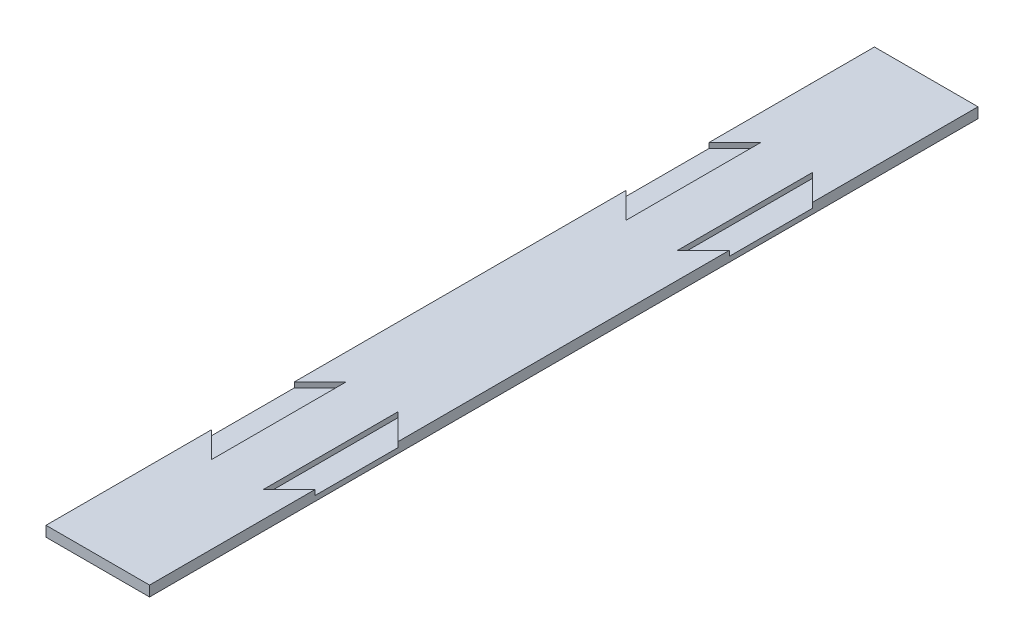
SolidWorks part; units mm, degrees
ref_plane "Front Plane" through (0, 0, 0) normal (0, 0, 1) x (1, 0, 0)
ref_plane "Top Plane" through (0, 0, 0) normal (0, 1, 0) x (1, 0, 0)
ref_plane "Right Plane" through (0, 0, 0) normal (1, 0, 0) x (0, 0, -1)
sketch "Sketch1" plane through (0, 0, 0) normal (0, 1, 0) x (1, 0, 0)
  line L1 (-12.7, -101.6) -> (12.7, -101.6)
  line L2 (-12.7, -101.6) -> (-12.7, 101.6)
  line L3 (-12.7, 101.6) -> (12.7, 101.6)
  line L4 (12.7, -101.6) -> (12.7, 101.6)
  line L5 (-12.7, -101.6) -> (12.7, 101.6) construction
  line L6 (-12.7, 101.6) -> (12.7, -101.6) construction
  point P0 (0, 0)
  dimension "D1" = 25.4
  dimension "D2" = 203.2
extrude "Boss-Extrude1" add sketch "Sketch1" against normal blind 2.54
sketch "Sketch3" plane through (0, 0, 0) normal (0, 1, 0) x (1, 0, 0)
  line L0 (12.7, 40.64) -> (6.35, 34.29)
  line L1 (12.7, -101.6) -> (12.7, 101.6) construction
  line L2 (6.35, 34.29) -> (6.35, 67.31)
  line L3 (6.35, 67.31) -> (12.7, 60.96)
  line L4 (12.7, 60.96) -> (12.7, 40.64)
  line L5 (12.7, 101.6) -> (-12.7, 101.6) construction
  line L6 (0, -1.397) -> (0, 1.397) construction
  line L7 (-6.35, 67.31) -> (-12.7, 60.96)
  line L8 (-6.35, 34.29) -> (-6.35, 67.31)
  line L9 (-12.7, 40.64) -> (-6.35, 34.29)
  line L10 (-12.7, 60.96) -> (-12.7, 40.64)
  line L11 (-1.397, 0) -> (1.397, 0) construction
  line L12 (6.35, -67.31) -> (12.7, -60.96)
  line L13 (6.35, -34.29) -> (6.35, -67.31)
  line L14 (12.7, -40.64) -> (6.35, -34.29)
  line L15 (12.7, -60.96) -> (12.7, -40.64)
  line L16 (-6.35, -34.29) -> (-6.35, -67.31)
  line L17 (-12.7, -40.64) -> (-6.35, -34.29)
  line L18 (-12.7, -60.96) -> (-12.7, -40.64)
  line L19 (-6.35, -67.31) -> (-12.7, -60.96)
  point P4 (6.35, 50.2533)
  point P7 (12.7, 50.8)
  dimension "D1" = 45
  dimension "D2" = 45
  dimension "D3" = 6.35
  dimension "D4" = 20.32
  dimension "D5" = 50.8
extrude "Cut-Extrude1" cut sketch "Sketch3" against normal blind 1.27
